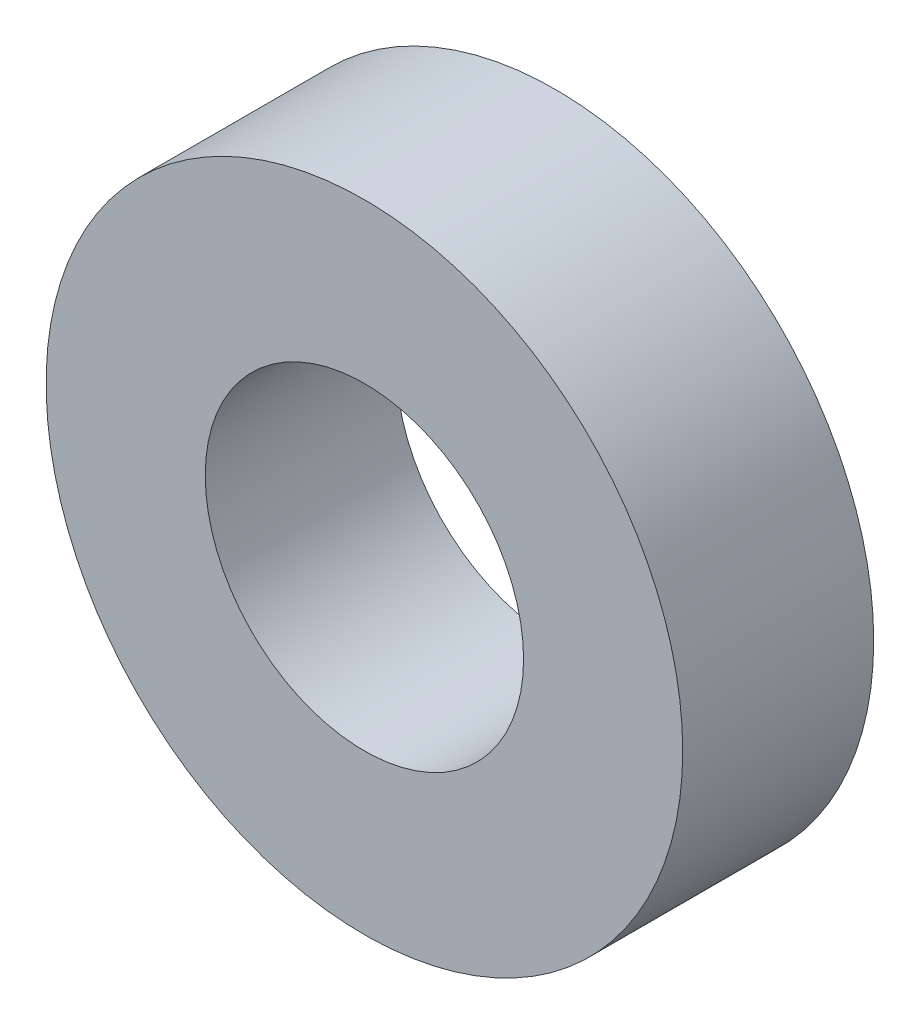
SolidWorks part; units mm, degrees
ref_plane "Front Plane" through (0, 0, 0) normal (0, 0, 1) x (1, 0, 0)
ref_plane "Top Plane" through (0, 0, 0) normal (0, 1, 0) x (1, 0, 0)
ref_plane "Right Plane" through (0, 0, 0) normal (1, 0, 0) x (0, 0, -1)
sketch "Sketch1" plane through (0, 0, 0) normal (0, 0, 1) x (1, 0, 0)
  circle A0 centre (0, 0) radius 5
  dimension "D1" = 10
extrude "Boss-Extrude1" add sketch "Sketch1" along normal blind 3
hole_wizard "Ø5.0mm Dowel Hole1" positions "Sketch2" profile "Sketch3" hole size "Ø5.0" standard "ANSI Metric" end condition up to next
sketch "Sketch2" plane through (0, 0, 3) normal (0, 0, 1) x (1, 0, 0)
  point P0 (0, 0)
sketch "Sketch3" plane through (0, 0, 3) normal (1, 0, 0) x (0, -1, 0)
  line L0 (0, 0) -> (0, 3)
  line L1 (0, 3) -> (2.5, 3)
  line L2 (2.5, 3) -> (2.5, 0)
  line L5 (2.5, 0) -> (0, 0)
  line L11 (0, -6.35) -> (0, 107.95) construction
  dimension "Thru Hole Dia." = 5
  dimension "Thru Hole Depth" = 3
